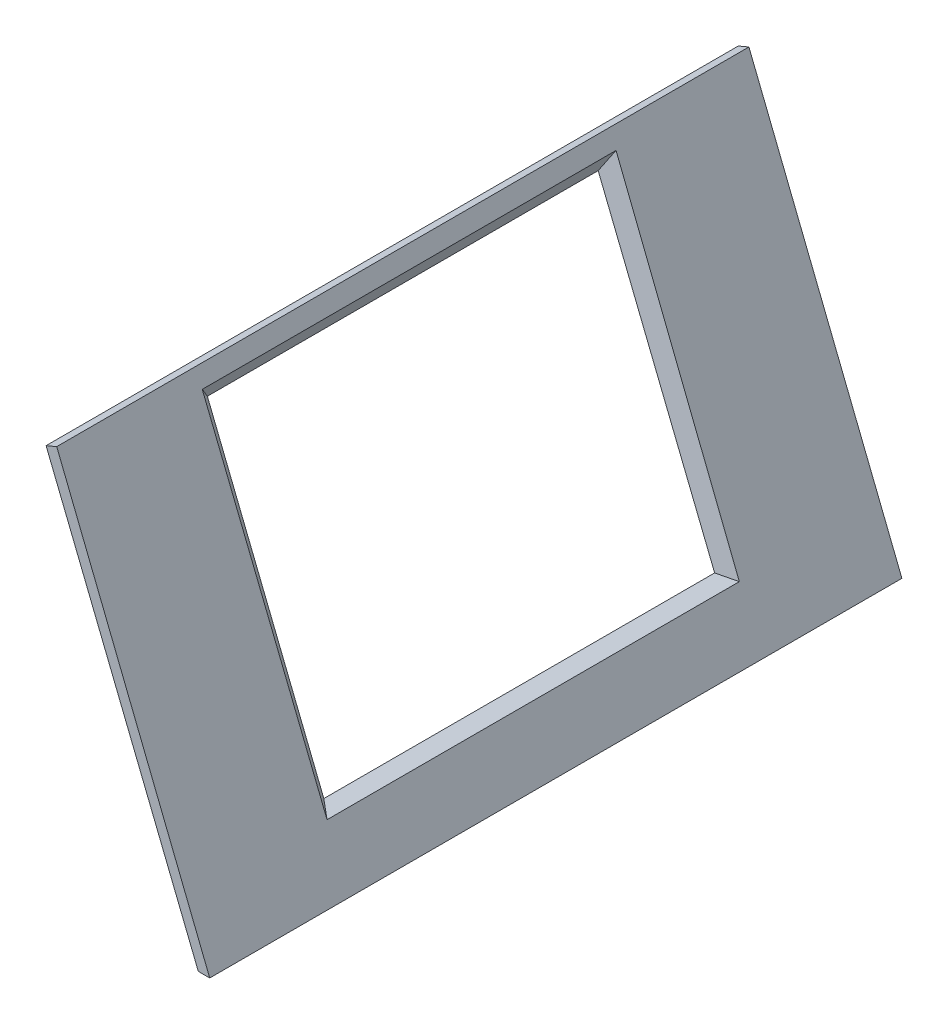
SolidWorks part; units mm, degrees
ref_plane "Plan de face" through (0, 0, 0) normal (0, 0, 1) x (1, 0, 0)
ref_plane "Plan de dessus" through (0, 0, 0) normal (0, 1, 0) x (1, 0, 0)
ref_plane "Plan de droite" through (0, 0, 0) normal (1, 0, 0) x (0, 0, -1)
sketch "Esquisse1" plane through (0, 0, 0) normal (0, 0, 1) x (1, 0, 0)
  line L0 (235.6068, 81.335) -> (103.6557, 410.0446)
  line L1 (103.6557, 410.0446) -> (112.8744, 413.9196)
  line L3 (112.8744, 413.9196) -> (245.5002, 81.335)
  line L4 (245.5002, 81.335) -> (235.6068, 81.335)
  dimension "D1" = 10
extrude "Boss.-Extru.1" add sketch "Esquisse1" along normal blind 600
sketch "Esquisse2" plane through (231.0287, 92.7398, 0) normal (-0.928, -0.3725, 0) x (0, 0, 1)
  line L1 (130.8597, 316.6615) -> (469.6057, 316.6615)
  line L2 (130.8597, 316.6615) -> (130.8597, 45.6615)
  line L3 (130.8597, 45.6615) -> (469.6057, 45.6615)
  line L4 (469.6057, 316.6615) -> (469.6057, 45.6615)
extrude "Enlèv. mat.-Extru.1" cut sketch "Esquisse2" against normal blind 10 draft 45 draft outward yes
